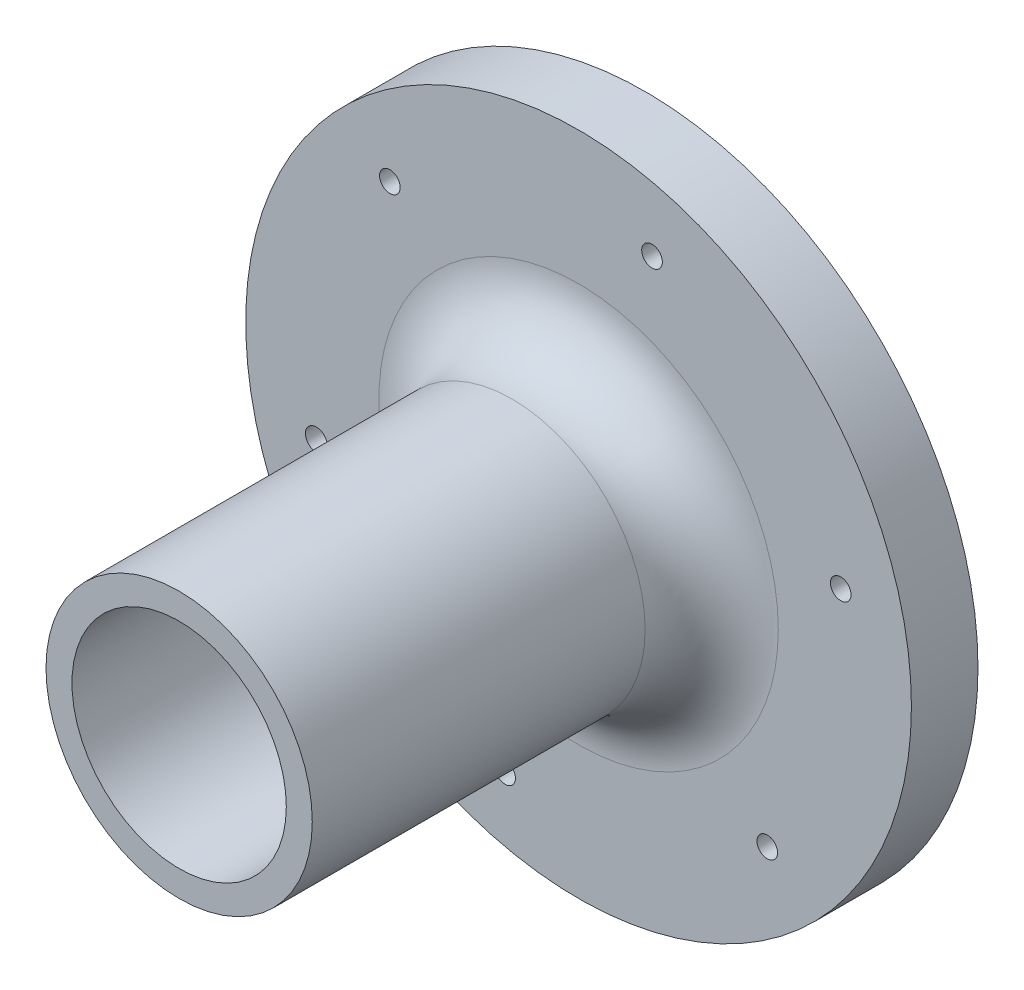
SolidWorks part; units mm, degrees
ref_plane "Front Plane" through (0, 0, 0) normal (0, 0, 1) x (1, 0, 0)
ref_plane "Top Plane" through (0, 0, 0) normal (0, 1, 0) x (1, 0, 0)
ref_plane "Right Plane" through (0, 0, 0) normal (1, 0, 0) x (0, 0, -1)
sketch "Sketch1" plane through (0, 0, 0) normal (0, 0, 1) x (1, 0, 0)
  circle A0 centre (0, 0) radius 50
  circle A7 centre (0, 0) radius 16.5
  circle A8 centre (-11.034, -39.0984) radius 1.55
  circle A9 centre (-39.3772, -9.9934) radius 1.6495
  circle A10 centre (-28.3431, 29.1049) radius 1.55
  circle A19 centre (11.034, 39.0984) radius 1.55
  circle A20 centre (39.3772, 9.9934) radius 1.55
  circle A21 centre (28.3431, -29.1049) radius 1.55
  point P18 (0, 0)
  point P20 (0, 0)
  point P36 (0, 0)
  dimension "D1" = 100
  dimension "D5" = 33
extrude "Boss-Extrude1" add sketch "Sketch1" along normal blind 10
sketch "Sketch2" plane through (0, 0, 10) normal (0, 0, 1) x (1, 0, 0)
  circle A0 centre (0, 0) radius 20
  circle A1 centre (0, 0) radius 16.1
  dimension "D1" = 40
  dimension "D2" = 32.2
extrude "Boss-Extrude2" add sketch "Sketch2" along normal blind 60
fillet "Fillet1" radius 10 1 edges at (20, 0, 10)
